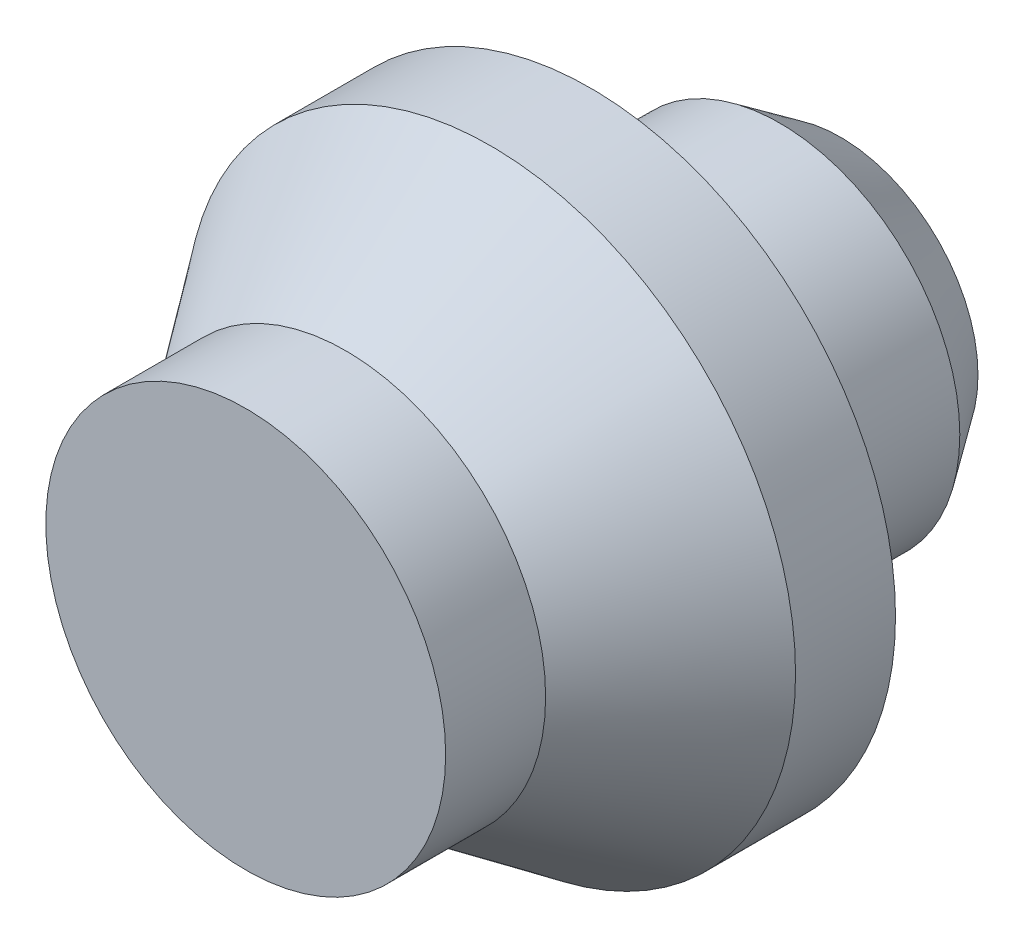
SolidWorks part; units mm, degrees
material "ABS"
ref_plane "Front Plane" through (0, 0, 0) normal (0, 0, 1) x (1, 0, 0)
ref_plane "Top Plane" through (0, 0, 0) normal (0, 1, 0) x (1, 0, 0)
ref_plane "Right Plane" through (0, 0, 0) normal (1, 0, 0) x (0, 0, -1)
sketch "Sketch1" plane through (0, 0, 0) normal (0, 1, 0) x (1, 0, 0)
  line L0 (0, 0) -> (0, 11.9)
  line L1 (0, 11.9) -> (2.75, 11.9)
  line L2 (2.75, 11.9) -> (3.6, 10.6861)
  line L3 (3.6, 10.6861) -> (3.6, 6.9)
  line L4 (3.6, 6.9) -> (6.1, 6.9)
  line L5 (6.1, 6.9) -> (6.1, 4.9)
  line L6 (6.1, 4.9) -> (4, 2)
  line L7 (4, 2) -> (4, 0)
  line L8 (4, 0) -> (0, 0)
  dimension "D1" = 6.9
  dimension "D2" = 3.6
  dimension "D3" = 2.75
  dimension "D4" = 2
  dimension "D5" = 2
  dimension "D6" = 4
  dimension "D7" = 5
  dimension "D8" = 145
  dimension "D9" = 2.5
revolve "Revolve1" add sketch "Sketch1" angle 360 about L0
